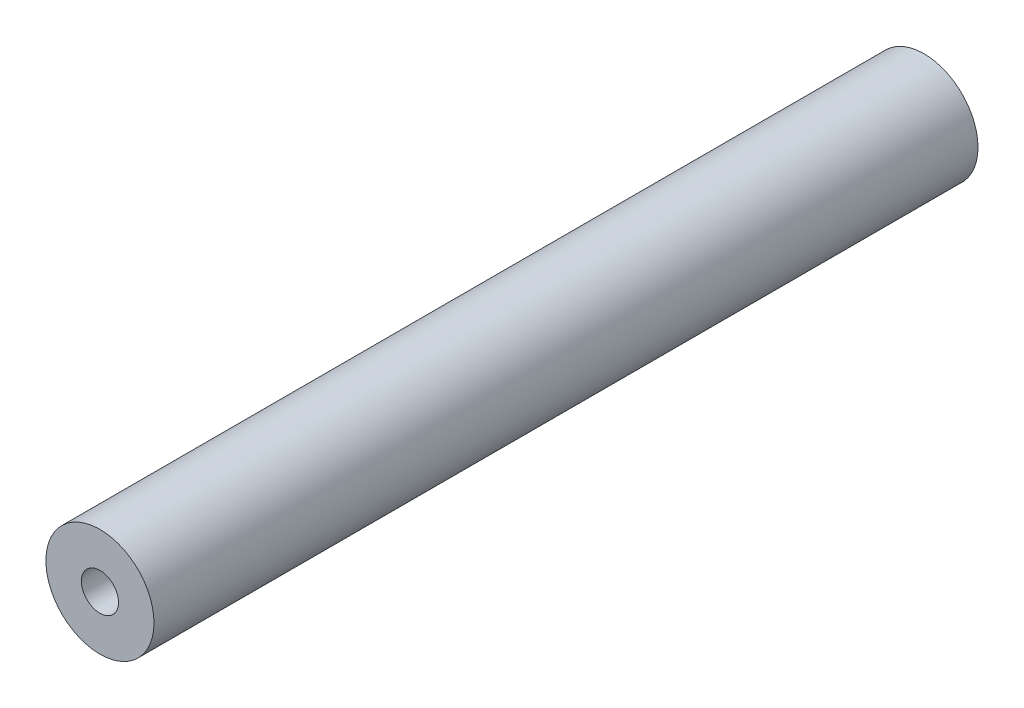
SolidWorks part; units mm, degrees
ref_plane "Front Plane" through (0, 0, 0) normal (0, 0, 1) x (1, 0, 0)
ref_plane "Top Plane" through (0, 0, 0) normal (0, 1, 0) x (1, 0, 0)
ref_plane "Right Plane" through (0, 0, 0) normal (1, 0, 0) x (0, 0, -1)
sketch "Sketch1" plane through (0, 0, 0) normal (0, 0, 1) x (1, 0, 0)
  circle A0 centre (0, 0) radius 4
  dimension "D1" = 8
extrude "Boss-Extrude1" add sketch "Sketch1" along normal blind 60.98
sketch "Sketch2" plane through (0, 0, 0) normal (0, 0, -1) x (-1, 0, 0)
  circle A0 centre (0, 0) radius 1.375
  dimension "D1" = 2.75
extrude "Cut-Extrude1" cut sketch "Sketch2" against normal through all
